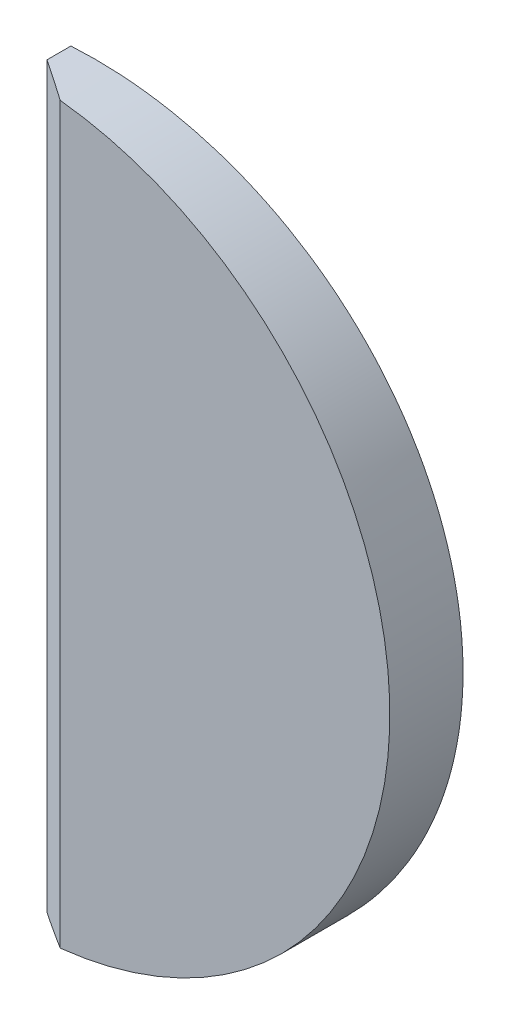
SolidWorks part; units mm, degrees
material "Стекло"
ref_plane "Front" through (0, 0, 0) normal (0, 0, 1) x (1, 0, 0)
ref_plane "Top" through (0, 0, 0) normal (0, 1, 0) x (1, 0, 0)
ref_plane "Right" through (0, 0, 0) normal (1, 0, 0) x (0, 0, -1)
sketch "Эскиз5" plane through (0, 0, 0) normal (1, 0, 0) x (0, 0, -1)
  line L0 (-4, 0) -> (-4, 15)
  line L1 (-2.303, 15) -> (-4, 15)
  line L2 (1, 0) -> (-4, 0) construction
  line L3 (0, 0) -> (-4, 0)
  line L4 (0, 0) -> (0, 13.3819) construction
  arc A0 (0, 0) -> (-2.303, 15) centre (-50, 0) ccw
  dimension "D3" = 50
  dimension "D1" = 4
  dimension "D2" = 30
revolve "Повернуть1" add sketch "Эскиз5" angle 360 about L2
sketch "Эскиз6" plane through (0, 0, 4) normal (0, 0, 1) x (1, 0, 0)
  line L0 (-3, 14) -> (-3, -14)
  line L1 (11, 0) -> (11, -14) construction
  arc A0 (-3, 14) -> (-3, -14) centre (-3, 0) cw
  circle A1 centre (0, 0) radius 15 construction
  dimension "D1" = 14
  dimension "D2" = 3
  dimension "D3" = 14
extrude "Вырез-Вытянуть1" cut sketch "Эскиз6" against normal through all
chamfer "Фаска1" distance 1 distance2 1.5 1 edges at (-3, 0, 4)
